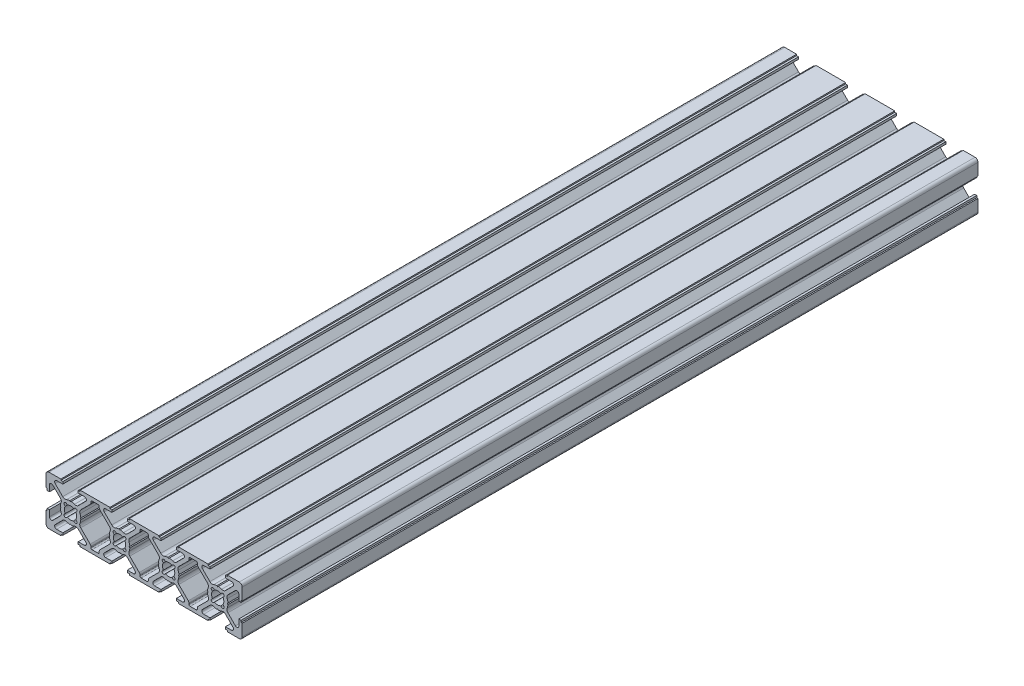
SolidWorks part; units mm, degrees
material "6063-T5"
ref_plane "Ön Düzlem" through (0, 0, 0) normal (0, 0, 1) x (1, 0, 0)
ref_plane "Üst Düzlem" through (0, 0, 0) normal (0, 1, 0) x (1, 0, 0)
ref_plane "Sağ Düzlem" through (0, 0, 0) normal (1, 0, 0) x (0, 0, -1)
sketch "Model" plane through (0, 0, 0) normal (0, 0, 1) x (1, 0, 0)
  line L0 (-8.8, -10) -> (-3.95, -10)
  line L1 (-3.95, -10) -> (-3.95, -9.5)
  line L2 (-3.95, -9.5) -> (-3.1475, -9.5)
  line L3 (-3.1475, -9.5) -> (-3.1475, -8.6)
  line L4 (-3.1475, -8.6) -> (-5.6787, -8.6)
  line L5 (-6.2444, -7.2343) -> (-3.1787, -4.1687)
  line L6 (-0.29, -4.19) -> (0, -3.9)
  line L7 (0, -3.9) -> (0.29, -4.19)
  line L8 (3.1768, -4.1667) -> (6.2444, -7.2343)
  line L9 (5.6787, -8.6) -> (3.1475, -8.6)
  line L10 (3.1475, -8.6) -> (3.1475, -9.5)
  line L11 (3.1475, -9.5) -> (3.95, -9.5)
  line L12 (3.95, -9.5) -> (3.95, -10)
  line L13 (3.95, -10) -> (16.05, -10)
  line L14 (16.05, -10) -> (16.05, -9.5)
  line L15 (16.05, -9.5) -> (16.8525, -9.5)
  line L16 (16.8525, -9.5) -> (16.8525, -8.6)
  line L17 (16.8525, -8.6) -> (14.3213, -8.6)
  line L18 (13.7556, -7.2343) -> (16.8213, -4.1687)
  line L19 (19.71, -4.19) -> (20, -3.9)
  line L20 (20, -3.9) -> (20.29, -4.19)
  line L21 (23.1768, -4.1667) -> (26.2444, -7.2343)
  line L22 (25.6787, -8.6) -> (23.1475, -8.6)
  line L23 (23.1475, -8.6) -> (23.1475, -9.5)
  line L24 (23.1475, -9.5) -> (23.95, -9.5)
  line L25 (23.95, -9.5) -> (23.95, -10)
  line L26 (23.95, -10) -> (36.05, -10)
  line L27 (36.05, -10) -> (36.05, -9.5)
  line L28 (36.05, -9.5) -> (36.8525, -9.5)
  line L29 (36.8525, -9.5) -> (36.8525, -8.6)
  line L30 (36.8525, -8.6) -> (34.3213, -8.6)
  line L31 (33.7556, -7.2343) -> (36.8213, -4.1687)
  line L32 (39.71, -4.19) -> (40, -3.9)
  line L33 (40, -3.9) -> (40.29, -4.19)
  line L34 (43.1768, -4.1667) -> (46.2444, -7.2343)
  line L35 (45.6787, -8.6) -> (43.1475, -8.6)
  line L36 (43.1475, -8.6) -> (43.1475, -9.5)
  line L37 (43.1475, -9.5) -> (43.95, -9.5)
  line L38 (43.95, -9.5) -> (43.95, -10)
  line L39 (43.95, -10) -> (56.05, -10)
  line L40 (56.05, -10) -> (56.05, -9.5)
  line L41 (56.05, -9.5) -> (56.8525, -9.5)
  line L42 (56.8525, -9.5) -> (56.8525, -8.6)
  line L43 (56.8525, -8.6) -> (54.3213, -8.6)
  line L44 (53.7556, -7.2343) -> (56.8213, -4.1687)
  line L45 (59.71, -4.19) -> (60, -3.9)
  line L46 (60, -3.9) -> (60.29, -4.19)
  line L47 (63.1768, -4.1667) -> (66.2444, -7.2343)
  line L48 (65.6787, -8.6) -> (63.1475, -8.6)
  line L49 (63.1475, -8.6) -> (63.1475, -9.5)
  line L50 (63.1475, -9.5) -> (63.95, -9.5)
  line L51 (63.95, -9.5) -> (63.95, -10)
  line L52 (63.95, -10) -> (68.8, -10)
  line L53 (70, -8.8) -> (70, -3.95)
  line L54 (70, -3.95) -> (69.5, -3.95)
  line L55 (69.5, -3.95) -> (69.5, -3.1477)
  line L56 (69.5, -3.1477) -> (68.6, -3.1477)
  line L57 (68.6, -3.1477) -> (68.6, -5.6787)
  line L58 (67.2343, -6.2444) -> (64.1687, -3.1787)
  line L59 (64.19, -0.29) -> (63.9, 0)
  line L60 (63.9, 0) -> (64.19, 0.29)
  line L61 (64.1667, 3.1768) -> (67.2343, 6.2444)
  line L62 (68.6, 5.6787) -> (68.6, 3.1475)
  line L63 (68.6, 3.1475) -> (69.5, 3.1475)
  line L64 (69.5, 3.1475) -> (69.5, 3.95)
  line L65 (69.5, 3.95) -> (70, 3.95)
  line L66 (70, 3.95) -> (70, 8.8)
  line L67 (68.8, 10) -> (63.95, 10)
  line L68 (63.95, 10) -> (63.95, 9.5)
  line L69 (63.95, 9.5) -> (63.1475, 9.5)
  line L70 (63.1475, 9.5) -> (63.1475, 8.6)
  line L71 (63.1475, 8.6) -> (65.6787, 8.6)
  line L72 (66.2444, 7.2343) -> (63.1768, 4.1667)
  line L73 (60.29, 4.19) -> (60, 3.9)
  line L74 (60, 3.9) -> (59.71, 4.19)
  line L75 (56.8213, 4.1687) -> (53.7556, 7.2343)
  line L76 (54.3213, 8.6) -> (56.8525, 8.6)
  line L77 (56.8525, 8.6) -> (56.8525, 9.5)
  line L78 (56.8525, 9.5) -> (56.05, 9.5)
  line L79 (56.05, 9.5) -> (56.05, 10)
  line L80 (56.05, 10) -> (43.95, 10)
  line L81 (43.95, 10) -> (43.95, 9.5)
  line L82 (43.95, 9.5) -> (43.1475, 9.5)
  line L83 (43.1475, 9.5) -> (43.1475, 8.6)
  line L84 (43.1475, 8.6) -> (45.6787, 8.6)
  line L85 (46.2444, 7.2343) -> (43.1768, 4.1667)
  line L86 (40.29, 4.19) -> (40, 3.9)
  line L87 (40, 3.9) -> (39.71, 4.19)
  line L88 (36.8213, 4.1687) -> (33.7556, 7.2343)
  line L89 (34.3213, 8.6) -> (36.8525, 8.6)
  line L90 (36.8525, 8.6) -> (36.8525, 9.5)
  line L91 (36.8525, 9.5) -> (36.05, 9.5)
  line L92 (36.05, 9.5) -> (36.05, 10)
  line L93 (36.05, 10) -> (23.95, 10)
  line L94 (23.95, 10) -> (23.95, 9.5)
  line L95 (23.95, 9.5) -> (23.1475, 9.5)
  line L96 (23.1475, 9.5) -> (23.1475, 8.6)
  line L97 (23.1475, 8.6) -> (25.6787, 8.6)
  line L98 (26.2444, 7.2343) -> (23.1768, 4.1667)
  line L99 (20.29, 4.19) -> (20, 3.9)
  line L100 (20, 3.9) -> (19.71, 4.19)
  line L101 (16.8213, 4.1687) -> (13.7556, 7.2343)
  line L102 (14.3213, 8.6) -> (16.8525, 8.6)
  line L103 (16.8525, 8.6) -> (16.8525, 9.5)
  line L104 (16.8525, 9.5) -> (16.05, 9.5)
  line L105 (16.05, 9.5) -> (16.05, 10)
  line L106 (16.05, 10) -> (3.95, 10)
  line L107 (3.95, 10) -> (3.95, 9.5)
  line L108 (3.95, 9.5) -> (3.1475, 9.5)
  line L109 (3.1475, 9.5) -> (3.1475, 8.6)
  line L110 (3.1475, 8.6) -> (5.6787, 8.6)
  line L111 (6.2444, 7.2343) -> (3.1768, 4.1667)
  line L112 (0.29, 4.19) -> (0, 3.9)
  line L113 (0, 3.9) -> (-0.29, 4.19)
  line L114 (-3.1787, 4.1687) -> (-6.2444, 7.2343)
  line L115 (-5.6787, 8.6) -> (-3.1475, 8.6)
  line L116 (-3.1475, 8.6) -> (-3.1475, 9.5)
  line L117 (-3.1475, 9.5) -> (-3.95, 9.5)
  line L118 (-3.95, 9.5) -> (-3.95, 10)
  line L119 (-3.95, 10) -> (-8.8, 10)
  line L120 (-10, 8.8) -> (-10, 3.95)
  line L121 (-10, 3.95) -> (-9.5, 3.95)
  line L122 (-9.5, 3.95) -> (-9.5, 3.1475)
  line L123 (-9.5, 3.1475) -> (-8.6, 3.1475)
  line L124 (-8.6, 3.1475) -> (-8.6, 5.6787)
  line L125 (-7.2343, 6.2444) -> (-4.1667, 3.1768)
  line L126 (-4.19, 0.29) -> (-3.9, 0)
  line L127 (-3.9, 0) -> (-4.19, -0.29)
  line L128 (-4.1687, -3.1787) -> (-7.2343, -6.2444)
  line L129 (-8.6, -5.6787) -> (-8.6, -3.1475)
  line L130 (-8.6, -3.1475) -> (-9.5, -3.1475)
  line L131 (-9.5, -3.1475) -> (-9.5, -3.95)
  line L132 (-9.5, -3.95) -> (-10, -3.95)
  line L133 (-10, -3.95) -> (-10, -8.8)
  line L134 (62.1404, 1.2918) -> (62.4749, 1.6263)
  line L135 (61.6263, 2.4749) -> (61.2918, 2.1404)
  line L136 (58.7082, 2.1404) -> (58.3737, 2.4749)
  line L137 (57.5251, 1.6263) -> (57.8596, 1.2918)
  line L138 (57.8596, -1.2918) -> (57.5251, -1.6263)
  line L139 (58.3737, -2.4749) -> (58.7082, -2.1404)
  line L140 (61.2918, -2.1404) -> (61.6263, -2.4749)
  line L141 (62.4749, -1.6263) -> (62.1404, -1.2918)
  line L142 (55.8342, -3.1759) -> (51.9899, -7.0201)
  line L143 (51.6971, -7.7272) -> (51.6971, -8.1)
  line L144 (51.1971, -8.6) -> (48.8029, -8.6)
  line L145 (48.3029, -8.1) -> (48.3029, -7.7272)
  line L146 (48.0101, -7.0201) -> (44.1658, -3.1759)
  line L147 (44.19, -0.29) -> (43.9, 0)
  line L148 (43.9, 0) -> (44.19, 0.29)
  line L149 (44.1658, 3.1759) -> (48.0101, 7.0201)
  line L150 (48.3029, 7.7272) -> (48.3029, 8.1)
  line L151 (48.8029, 8.6) -> (51.1971, 8.6)
  line L152 (51.6971, 8.1) -> (51.6971, 7.7272)
  line L153 (51.9899, 7.0201) -> (55.8342, 3.1759)
  line L154 (55.81, 0.29) -> (56.1, 0)
  line L155 (56.1, 0) -> (55.81, -0.29)
  line L156 (-2.1404, 1.2918) -> (-2.4749, 1.6263)
  line L157 (-1.6263, 2.4749) -> (-1.2918, 2.1404)
  line L158 (1.2918, 2.1404) -> (1.6263, 2.4749)
  line L159 (2.4749, 1.6263) -> (2.1404, 1.2918)
  line L160 (2.1404, -1.2918) -> (2.4749, -1.6263)
  line L161 (1.6263, -2.4749) -> (1.2918, -2.1404)
  line L162 (-1.2918, -2.1404) -> (-1.6263, -2.4749)
  line L163 (-2.4749, -1.6263) -> (-2.1404, -1.2918)
  line L164 (4.1658, -3.1759) -> (8.0101, -7.0201)
  line L165 (8.3029, -7.7272) -> (8.3029, -8.1)
  line L166 (8.8029, -8.6) -> (11.1971, -8.6)
  line L167 (11.6971, -8.1) -> (11.6971, -7.7272)
  line L168 (11.9899, -7.0201) -> (15.8342, -3.1759)
  line L169 (15.81, -0.29) -> (16.1, 0)
  line L170 (16.1, 0) -> (15.81, 0.29)
  line L171 (15.8342, 3.1759) -> (11.9899, 7.0201)
  line L172 (11.6971, 7.7272) -> (11.6971, 8.1)
  line L173 (11.1971, 8.6) -> (8.8029, 8.6)
  line L174 (8.3029, 8.1) -> (8.3029, 7.7272)
  line L175 (8.0101, 7.0201) -> (4.1658, 3.1759)
  line L176 (4.19, 0.29) -> (3.9, 0)
  line L177 (3.9, 0) -> (4.19, -0.29)
  line L178 (17.8596, 1.2918) -> (17.5251, 1.6263)
  line L179 (18.3737, 2.4749) -> (18.7082, 2.1404)
  line L180 (21.2918, 2.1404) -> (21.6263, 2.4749)
  line L181 (22.4749, 1.6263) -> (22.1404, 1.2918)
  line L182 (22.1404, -1.2918) -> (22.4749, -1.6263)
  line L183 (21.6263, -2.4749) -> (21.2918, -2.1404)
  line L184 (18.7082, -2.1404) -> (18.3737, -2.4749)
  line L185 (17.5251, -1.6263) -> (17.8596, -1.2918)
  line L186 (37.8596, 1.2918) -> (37.5251, 1.6263)
  line L187 (38.3737, 2.4749) -> (38.7082, 2.1404)
  line L188 (41.2918, 2.1404) -> (41.6263, 2.4749)
  line L189 (42.4749, 1.6263) -> (42.1404, 1.2918)
  line L190 (42.1404, -1.2918) -> (42.4749, -1.6263)
  line L191 (41.6263, -2.4749) -> (41.2918, -2.1404)
  line L192 (38.7082, -2.1404) -> (38.3737, -2.4749)
  line L193 (37.5251, -1.6263) -> (37.8596, -1.2918)
  line L194 (24.1658, -3.1759) -> (28.0101, -7.0201)
  line L195 (28.3029, -7.7272) -> (28.3029, -8.1)
  line L196 (28.8029, -8.6) -> (31.1971, -8.6)
  line L197 (31.6971, -8.1) -> (31.6971, -7.7272)
  line L198 (31.9899, -7.0201) -> (35.8342, -3.1759)
  line L199 (35.81, -0.29) -> (36.1, 0)
  line L200 (36.1, 0) -> (35.81, 0.29)
  line L201 (35.8342, 3.1759) -> (31.9899, 7.0201)
  line L202 (31.6971, 7.7272) -> (31.6971, 8.1)
  line L203 (31.1971, 8.6) -> (28.8029, 8.6)
  line L204 (28.3029, 8.1) -> (28.3029, 7.7272)
  line L205 (28.0101, 7.0201) -> (24.1658, 3.1759)
  line L206 (24.19, 0.29) -> (23.9, 0)
  line L207 (23.9, 0) -> (24.19, -0.29)
  arc A0 (-6.2444, -7.2343) -> (-5.6787, -8.6) centre (-5.6787, -7.8) ccw
  arc A1 (-1.6394, -3.8668) -> (-3.1787, -4.1687) centre (-2.1845, -5.1629) ccw
  arc A2 (-1.6394, -3.8668) -> (-0.29, -4.19) centre (0, 0) ccw
  arc A3 (0.29, -4.19) -> (1.6394, -3.8668) centre (0, 0) ccw
  arc A4 (3.1768, -4.1667) -> (1.6394, -3.8668) centre (2.1855, -5.1581) ccw
  arc A5 (5.6787, -8.6) -> (6.2444, -7.2343) centre (5.6787, -7.8) ccw
  arc A6 (13.7556, -7.2343) -> (14.3213, -8.6) centre (14.3213, -7.8) ccw
  arc A7 (18.3606, -3.8668) -> (16.8213, -4.1687) centre (17.8155, -5.1629) ccw
  arc A8 (18.3606, -3.8668) -> (19.71, -4.19) centre (20, 0) ccw
  arc A9 (20.29, -4.19) -> (21.6394, -3.8668) centre (20, 0) ccw
  arc A10 (23.1768, -4.1667) -> (21.6394, -3.8668) centre (22.1855, -5.1581) ccw
  arc A11 (25.6787, -8.6) -> (26.2444, -7.2343) centre (25.6787, -7.8) ccw
  arc A12 (33.7556, -7.2343) -> (34.3213, -8.6) centre (34.3213, -7.8) ccw
  arc A13 (38.3606, -3.8668) -> (36.8213, -4.1687) centre (37.8155, -5.1629) ccw
  arc A14 (38.3606, -3.8668) -> (39.71, -4.19) centre (40, 0) ccw
  arc A15 (40.29, -4.19) -> (41.6394, -3.8668) centre (40, 0) ccw
  arc A16 (43.1768, -4.1667) -> (41.6394, -3.8668) centre (42.1855, -5.1581) ccw
  arc A17 (45.6787, -8.6) -> (46.2444, -7.2343) centre (45.6787, -7.8) ccw
  arc A18 (53.7556, -7.2343) -> (54.3213, -8.6) centre (54.3213, -7.8) ccw
  arc A19 (58.3606, -3.8668) -> (56.8213, -4.1687) centre (57.8155, -5.1629) ccw
  arc A20 (58.3606, -3.8668) -> (59.71, -4.19) centre (60, 0) ccw
  arc A21 (60.29, -4.19) -> (61.6394, -3.8668) centre (60, 0) ccw
  arc A22 (63.1768, -4.1667) -> (61.6394, -3.8668) centre (62.1855, -5.1581) ccw
  arc A23 (65.6787, -8.6) -> (66.2444, -7.2343) centre (65.6787, -7.8) ccw
  arc A24 (68.8, -10) -> (70, -8.8) centre (68.8, -8.8) ccw
  arc A25 (67.2343, -6.2444) -> (68.6, -5.6787) centre (67.8, -5.6787) ccw
  arc A26 (63.8668, -1.6394) -> (64.1687, -3.1787) centre (65.1629, -2.1845) ccw
  arc A27 (63.8668, -1.6394) -> (64.19, -0.29) centre (60, 0) ccw
  arc A28 (64.19, 0.29) -> (63.8668, 1.6394) centre (60, 0) ccw
  arc A29 (64.1667, 3.1768) -> (63.8668, 1.6394) centre (65.1581, 2.1855) ccw
  arc A30 (68.6, 5.6787) -> (67.2343, 6.2444) centre (67.8, 5.6787) ccw
  arc A31 (70, 8.8) -> (68.8, 10) centre (68.8, 8.8) ccw
  arc A32 (66.2444, 7.2343) -> (65.6787, 8.6) centre (65.6787, 7.8) ccw
  arc A33 (61.6394, 3.8668) -> (63.1768, 4.1667) centre (62.1855, 5.1581) ccw
  arc A34 (61.6394, 3.8668) -> (60.29, 4.19) centre (60, 0) ccw
  arc A35 (59.71, 4.19) -> (58.3606, 3.8668) centre (60, 0) ccw
  arc A36 (56.8213, 4.1687) -> (58.3606, 3.8668) centre (57.8155, 5.1629) ccw
  arc A37 (54.3213, 8.6) -> (53.7556, 7.2343) centre (54.3213, 7.8) ccw
  arc A38 (46.2444, 7.2343) -> (45.6787, 8.6) centre (45.6787, 7.8) ccw
  arc A39 (41.6394, 3.8668) -> (43.1768, 4.1667) centre (42.1855, 5.1581) ccw
  arc A40 (41.6394, 3.8668) -> (40.29, 4.19) centre (40, 0) ccw
  arc A41 (39.71, 4.19) -> (38.3606, 3.8668) centre (40, 0) ccw
  arc A42 (36.8213, 4.1687) -> (38.3606, 3.8668) centre (37.8155, 5.1629) ccw
  arc A43 (34.3213, 8.6) -> (33.7556, 7.2343) centre (34.3213, 7.8) ccw
  arc A44 (26.2444, 7.2343) -> (25.6787, 8.6) centre (25.6787, 7.8) ccw
  arc A45 (21.6394, 3.8668) -> (23.1768, 4.1667) centre (22.1855, 5.1581) ccw
  arc A46 (21.6394, 3.8668) -> (20.29, 4.19) centre (20, 0) ccw
  arc A47 (19.71, 4.19) -> (18.3606, 3.8668) centre (20, 0) ccw
  arc A48 (16.8213, 4.1687) -> (18.3606, 3.8668) centre (17.8155, 5.1629) ccw
  arc A49 (14.3213, 8.6) -> (13.7556, 7.2343) centre (14.3213, 7.8) ccw
  arc A50 (6.2444, 7.2343) -> (5.6787, 8.6) centre (5.6787, 7.8) ccw
  arc A51 (1.6394, 3.8668) -> (3.1768, 4.1667) centre (2.1855, 5.1581) ccw
  arc A52 (1.6394, 3.8668) -> (0.29, 4.19) centre (0, 0) ccw
  arc A53 (-0.29, 4.19) -> (-1.6394, 3.8668) centre (0, 0) ccw
  arc A54 (-3.1787, 4.1687) -> (-1.6394, 3.8668) centre (-2.1845, 5.1629) ccw
  arc A55 (-5.6787, 8.6) -> (-6.2444, 7.2343) centre (-5.6787, 7.8) ccw
  arc A56 (-8.8, 10) -> (-10, 8.8) centre (-8.8, 8.8) ccw
  arc A57 (-7.2343, 6.2444) -> (-8.6, 5.6787) centre (-7.8, 5.6787) ccw
  arc A58 (-3.8668, 1.6394) -> (-4.1667, 3.1768) centre (-5.1581, 2.1855) ccw
  arc A59 (-3.8668, 1.6394) -> (-4.19, 0.29) centre (0, 0) ccw
  arc A60 (-4.19, -0.29) -> (-3.8668, -1.6394) centre (0, 0) ccw
  arc A61 (-4.1687, -3.1787) -> (-3.8668, -1.6394) centre (-5.1629, -2.1845) ccw
  arc A62 (-8.6, -5.6787) -> (-7.2343, -6.2444) centre (-7.8, -5.6787) ccw
  arc A63 (-10, -8.8) -> (-8.8, -10) centre (-8.8, -8.8) ccw
  arc A64 (51.9899, -7.0201) -> (51.6971, -7.7272) centre (52.6971, -7.7272) ccw
  arc A65 (51.1971, -8.6) -> (51.6971, -8.1) centre (51.1971, -8.1) ccw
  arc A66 (48.3029, -8.1) -> (48.8029, -8.6) centre (48.8029, -8.1) ccw
  arc A67 (48.3029, -7.7272) -> (48.0101, -7.0201) centre (47.3029, -7.7272) ccw
  arc A68 (43.8668, -1.6394) -> (44.1658, -3.1759) centre (45.1558, -2.1859) ccw
  arc A69 (43.8668, -1.6394) -> (44.19, -0.29) centre (40, 0) ccw
  arc A70 (44.19, 0.29) -> (43.8668, 1.6394) centre (40, 0) ccw
  arc A71 (44.1658, 3.1759) -> (43.8668, 1.6394) centre (45.1558, 2.1859) ccw
  arc A72 (48.0101, 7.0201) -> (48.3029, 7.7272) centre (47.3029, 7.7272) ccw
  arc A73 (48.8029, 8.6) -> (48.3029, 8.1) centre (48.8029, 8.1) ccw
  arc A74 (51.6971, 8.1) -> (51.1971, 8.6) centre (51.1971, 8.1) ccw
  arc A75 (51.6971, 7.7272) -> (51.9899, 7.0201) centre (52.6971, 7.7272) ccw
  arc A76 (56.1332, 1.6394) -> (55.8342, 3.1759) centre (54.8442, 2.1859) ccw
  arc A77 (56.1332, 1.6394) -> (55.81, 0.29) centre (60, 0) ccw
  arc A78 (55.81, -0.29) -> (56.1332, -1.6394) centre (60, 0) ccw
  arc A79 (55.8342, -3.1759) -> (56.1332, -1.6394) centre (54.8442, -2.1859) ccw
  arc A80 (8.3029, -7.7272) -> (8.0101, -7.0201) centre (7.3029, -7.7272) ccw
  arc A81 (8.3029, -8.1) -> (8.8029, -8.6) centre (8.8029, -8.1) ccw
  arc A82 (11.1971, -8.6) -> (11.6971, -8.1) centre (11.1971, -8.1) ccw
  arc A83 (11.9899, -7.0201) -> (11.6971, -7.7272) centre (12.6971, -7.7272) ccw
  arc A84 (15.8342, -3.1759) -> (16.1332, -1.6394) centre (14.8442, -2.1859) ccw
  arc A85 (15.81, -0.29) -> (16.1332, -1.6394) centre (20, 0) ccw
  arc A86 (16.1332, 1.6394) -> (15.81, 0.29) centre (20, 0) ccw
  arc A87 (16.1332, 1.6394) -> (15.8342, 3.1759) centre (14.8442, 2.1859) ccw
  arc A88 (11.6971, 7.7272) -> (11.9899, 7.0201) centre (12.6971, 7.7272) ccw
  arc A89 (11.6971, 8.1) -> (11.1971, 8.6) centre (11.1971, 8.1) ccw
  arc A90 (8.8029, 8.6) -> (8.3029, 8.1) centre (8.8029, 8.1) ccw
  arc A91 (8.0101, 7.0201) -> (8.3029, 7.7272) centre (7.3029, 7.7272) ccw
  arc A92 (4.1658, 3.1759) -> (3.8668, 1.6394) centre (5.1558, 2.1859) ccw
  arc A93 (4.19, 0.29) -> (3.8668, 1.6394) centre (0, 0) ccw
  arc A94 (3.8668, -1.6394) -> (4.19, -0.29) centre (0, 0) ccw
  arc A95 (3.8668, -1.6394) -> (4.1658, -3.1759) centre (5.1558, -2.1859) ccw
  arc A96 (28.3029, -7.7272) -> (28.0101, -7.0201) centre (27.3029, -7.7272) ccw
  arc A97 (28.3029, -8.1) -> (28.8029, -8.6) centre (28.8029, -8.1) ccw
  arc A98 (31.1971, -8.6) -> (31.6971, -8.1) centre (31.1971, -8.1) ccw
  arc A99 (31.9899, -7.0201) -> (31.6971, -7.7272) centre (32.6971, -7.7272) ccw
  arc A100 (35.8342, -3.1759) -> (36.1332, -1.6394) centre (34.8442, -2.1859) ccw
  arc A101 (35.81, -0.29) -> (36.1332, -1.6394) centre (40, 0) ccw
  arc A102 (36.1332, 1.6394) -> (35.81, 0.29) centre (40, 0) ccw
  arc A103 (36.1332, 1.6394) -> (35.8342, 3.1759) centre (34.8442, 2.1859) ccw
  arc A104 (31.6971, 7.7272) -> (31.9899, 7.0201) centre (32.6971, 7.7272) ccw
  arc A105 (31.6971, 8.1) -> (31.1971, 8.6) centre (31.1971, 8.1) ccw
  arc A106 (28.8029, 8.6) -> (28.3029, 8.1) centre (28.8029, 8.1) ccw
  arc A107 (28.0101, 7.0201) -> (28.3029, 7.7272) centre (27.3029, 7.7272) ccw
  arc A108 (24.1658, 3.1759) -> (23.8668, 1.6394) centre (25.1558, 2.1859) ccw
  arc A109 (24.19, 0.29) -> (23.8668, 1.6394) centre (20, 0) ccw
  arc A110 (23.8668, -1.6394) -> (24.19, -0.29) centre (20, 0) ccw
  arc A111 (23.8668, -1.6394) -> (24.1658, -3.1759) centre (25.1558, -2.1859) ccw
  arc A112 (62.4749, 1.6263) -> (61.6263, 2.4749) centre (62.0506, 2.0506) ccw
  arc A113 (61.2918, 2.1404) -> (58.7082, 2.1404) centre (60, 0) ccw
  arc A114 (58.3737, 2.4749) -> (57.5251, 1.6263) centre (57.9494, 2.0506) ccw
  arc A115 (57.8596, 1.2918) -> (57.8596, -1.2918) centre (60, 0) ccw
  arc A116 (57.5251, -1.6263) -> (58.3737, -2.4749) centre (57.9494, -2.0506) ccw
  arc A117 (58.7082, -2.1404) -> (61.2918, -2.1404) centre (60, 0) ccw
  arc A118 (61.6263, -2.4749) -> (62.4749, -1.6263) centre (62.0506, -2.0506) ccw
  arc A119 (62.1404, -1.2918) -> (62.1404, 1.2918) centre (60, 0) ccw
  arc A120 (-1.6263, 2.4749) -> (-2.4749, 1.6263) centre (-2.0506, 2.0506) ccw
  arc A121 (1.2918, 2.1404) -> (-1.2918, 2.1404) centre (0, 0) ccw
  arc A122 (2.4749, 1.6263) -> (1.6263, 2.4749) centre (2.0506, 2.0506) ccw
  arc A123 (2.1404, -1.2918) -> (2.1404, 1.2918) centre (0, 0) ccw
  arc A124 (1.6263, -2.4749) -> (2.4749, -1.6263) centre (2.0506, -2.0506) ccw
  arc A125 (-1.2918, -2.1404) -> (1.2918, -2.1404) centre (0, 0) ccw
  arc A126 (-2.4749, -1.6263) -> (-1.6263, -2.4749) centre (-2.0506, -2.0506) ccw
  arc A127 (-2.1404, 1.2918) -> (-2.1404, -1.2918) centre (0, 0) ccw
  arc A128 (18.3737, 2.4749) -> (17.5251, 1.6263) centre (17.9494, 2.0506) ccw
  arc A129 (21.2918, 2.1404) -> (18.7082, 2.1404) centre (20, 0) ccw
  arc A130 (22.4749, 1.6263) -> (21.6263, 2.4749) centre (22.0506, 2.0506) ccw
  arc A131 (22.1404, -1.2918) -> (22.1404, 1.2918) centre (20, 0) ccw
  arc A132 (21.6263, -2.4749) -> (22.4749, -1.6263) centre (22.0506, -2.0506) ccw
  arc A133 (18.7082, -2.1404) -> (21.2918, -2.1404) centre (20, 0) ccw
  arc A134 (17.5251, -1.6263) -> (18.3737, -2.4749) centre (17.9494, -2.0506) ccw
  arc A135 (17.8596, 1.2918) -> (17.8596, -1.2918) centre (20, 0) ccw
  arc A136 (38.3737, 2.4749) -> (37.5251, 1.6263) centre (37.9494, 2.0506) ccw
  arc A137 (41.2918, 2.1404) -> (38.7082, 2.1404) centre (40, 0) ccw
  arc A138 (42.4749, 1.6263) -> (41.6263, 2.4749) centre (42.0506, 2.0506) ccw
  arc A139 (42.1404, -1.2918) -> (42.1404, 1.2918) centre (40, 0) ccw
  arc A140 (41.6263, -2.4749) -> (42.4749, -1.6263) centre (42.0506, -2.0506) ccw
  arc A141 (38.7082, -2.1404) -> (41.2918, -2.1404) centre (40, 0) ccw
  arc A142 (37.5251, -1.6263) -> (38.3737, -2.4749) centre (37.9494, -2.0506) ccw
  arc A143 (37.8596, 1.2918) -> (37.8596, -1.2918) centre (40, 0) ccw
extrude "Yükseklik-Ekstrüzyon1" add sketch "Model" against normal blind 300
